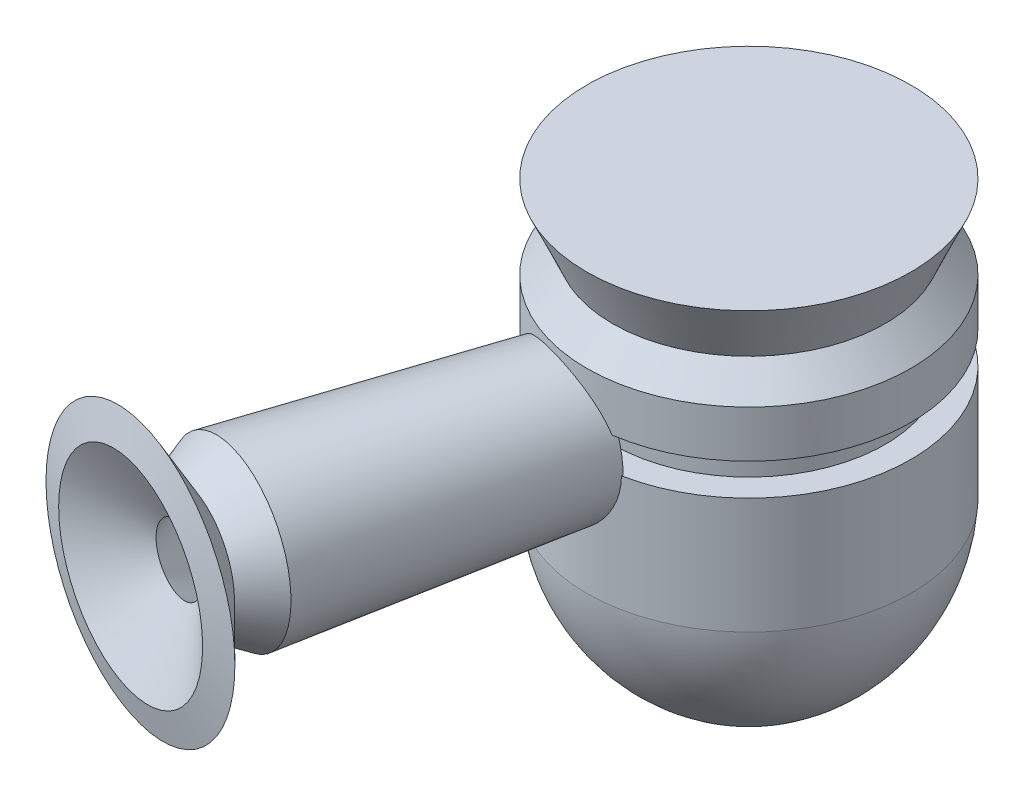
SolidWorks part; units mm, degrees
ref_plane "Front Plane" through (0, 0, 0) normal (0, 0, 1) x (1, 0, 0)
ref_plane "Top Plane" through (0, 0, 0) normal (0, 1, 0) x (1, 0, 0)
ref_plane "Right Plane" through (0, 0, 0) normal (1, 0, 0) x (0, 0, -1)
sketch "Sketch1" plane through (0, 0, 0) normal (0, 0, 1) x (1, 0, 0)
  line L4 (18.6543, 67.5095) -> (18.6543, 85.9517)
  line L5 (18.6543, 85.9517) -> (14.5542, 85.9517)
  line L14 (14.5542, 85.9517) -> (14.5542, 91.0387)
  line L15 (14.5542, 91.0387) -> (18.6543, 91.0387)
  line L16 (18.6543, 91.0387) -> (18.6543, 98.4877)
  line L17 (18.6543, 98.4877) -> (14.5542, 102.5878)
  line L18 (14.5542, 102.5878) -> (18.6543, 111.7505)
  line L19 (18.6543, 111.7505) -> (-7.1083, 111.7505)
  line L20 (-7.1083, 111.7505) -> (-7.1083, 98.4877)
  line L21 (-7.1083, 98.4877) -> (7.9965, 98.4877)
  line L22 (7.9965, 98.4877) -> (7.9965, 57.4276)
  line L23 (7.9965, 57.4276) -> (0.4441, 57.4276)
  line L24 (0.4441, 57.4276) -> (0.4441, 44.8657)
  line L25 (0.4441, 44.8657) -> (4.926, 44.8657)
  arc A0 (4.926, 44.8657) -> (18.6543, 67.5095) centre (-10.0159, 69.408) ccw
revolve "Revolve1" add sketch "Sketch1" angle 360 about L20
sketch "Sketch2" plane through (0, 85.9517, 0) normal (0, 1, 0) x (1, 0, 0)
  line L0 (-12.9416, -21.9389) -> (-23.9964, -19.4552)
  line L3 (-23.9964, -19.4552) -> (-36.865, -62.159)
  line L5 (-36.865, -62.159) -> (-35.0969, -68.2607)
  line L6 (-35.0969, -68.2607) -> (-47.1107, -71.7419)
  line L7 (-47.1107, -71.7419) -> (-42.6311, -74.2087)
  line L8 (-42.6311, -74.2087) -> (-30.6194, -70.7281)
  line L9 (-30.6194, -70.7281) -> (-32.8022, -63.1952)
  line L10 (-32.8022, -63.1952) -> (-20.4608, -37.5585)
  line L11 (-12.9416, -21.9389) -> (-17.1413, -38.4051)
  line L12 (-17.1413, -38.4051) -> (-20.4608, -37.5585)
  circle A0 centre (-7.1083, 0) radius 25.7626 construction
revolve "Revolve2" add sketch "Sketch2" angle 360 about L11
